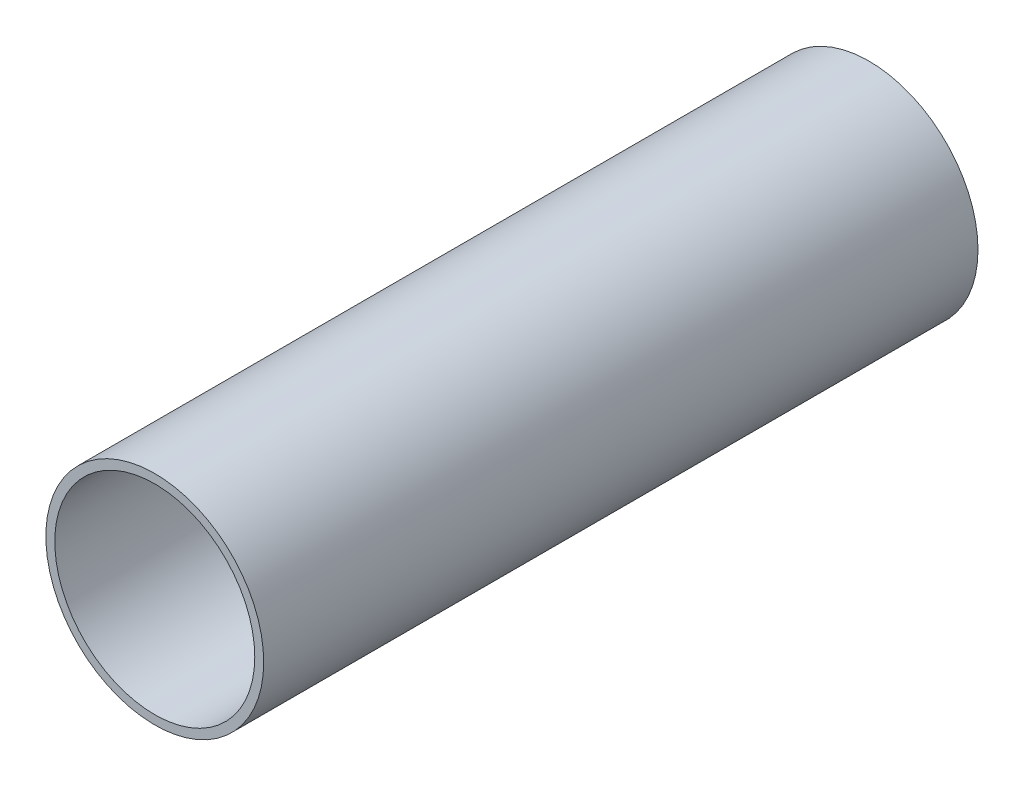
SolidWorks part; units mm, degrees
ref_plane "前视基准面" through (0, 0, 0) normal (0, 0, 1) x (1, 0, 0)
ref_plane "上视基准面" through (0, 0, 0) normal (0, 1, 0) x (1, 0, 0)
ref_plane "右视基准面" through (0, 0, 0) normal (1, 0, 0) x (0, 0, -1)
sketch "草图1" plane through (0, 0, 0) normal (0, 0, 1) x (1, 0, 0)
  circle A0 centre (0, 0) radius 15.25
  circle A1 centre (0, 0) radius 14
extrude "凸台-拉伸1" add sketch "草图1" along normal mid plane 100
